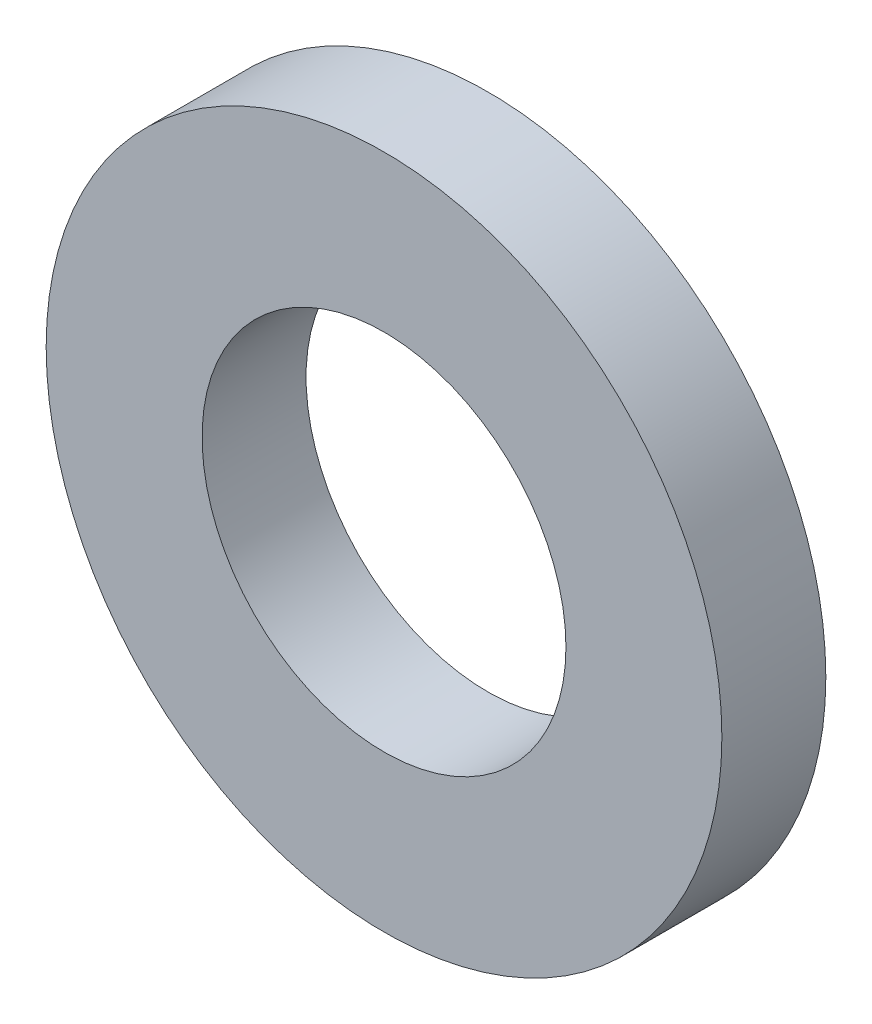
SolidWorks part; units mm, degrees
material "PVC Rigid"
ref_plane "Front Plane" through (0, 0, 0) normal (0, 0, 1) x (1, 0, 0)
ref_plane "Top Plane" through (0, 0, 0) normal (0, 1, 0) x (1, 0, 0)
ref_plane "Right Plane" through (0, 0, 0) normal (1, 0, 0) x (0, 0, -1)
sketch "Sketch1" plane through (0, 0, 0) normal (0, 0, 1) x (1, 0, 0)
  circle A0 centre (0, 0) radius 7
  circle A1 centre (0, 0) radius 13
  dimension "D1" = 14
  dimension "D2" = 26
extrude "Boss-Extrude1" add sketch "Sketch1" along normal blind 4
